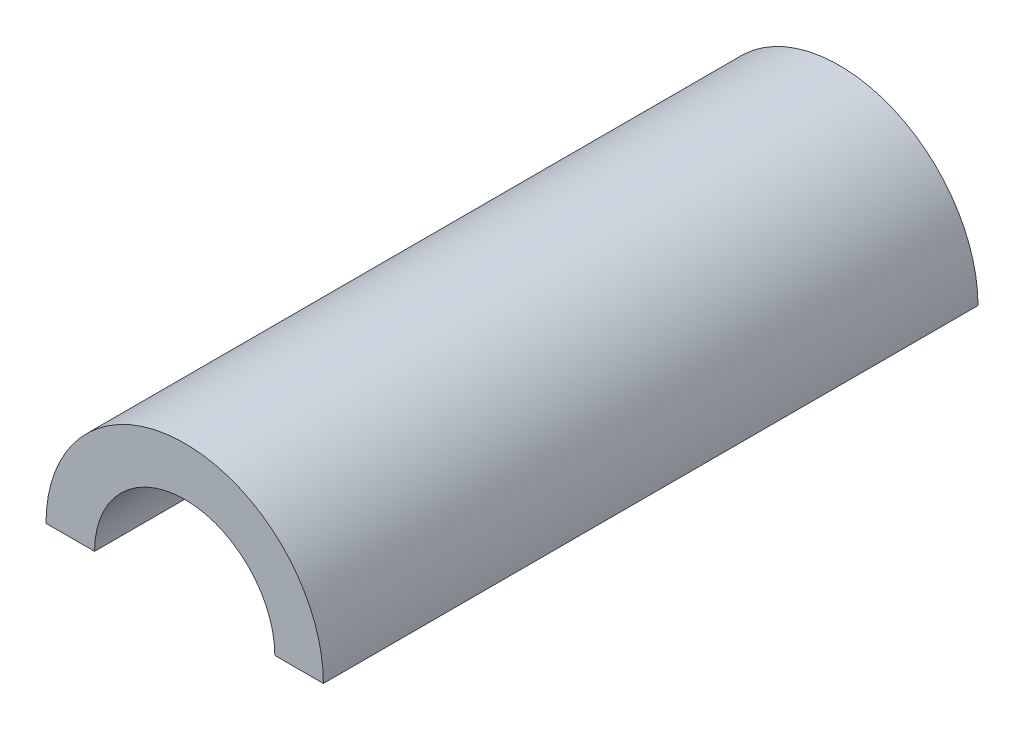
SolidWorks part; units mm, degrees
material "Aluminum Bronze"
ref_plane "Front Plane" through (0, 0, 0) normal (0, 0, 1) x (1, 0, 0)
ref_plane "Top Plane" through (0, 0, 0) normal (0, 1, 0) x (1, 0, 0)
ref_plane "Right Plane" through (0, 0, 0) normal (1, 0, 0) x (0, 0, -1)
sketch "Sketch2" plane through (0, 0, 0) normal (0, 0, 1) x (1, 0, 0)
  line L0 (10, 0) -> (-10, 0)
  circle A0 centre (0, 0) radius 6.5
  circle A1 centre (0, 0) radius 10
extrude "Boss-Extrude1" add sketch "Sketch2" along normal blind 47.2 contours L0 A1 A0
